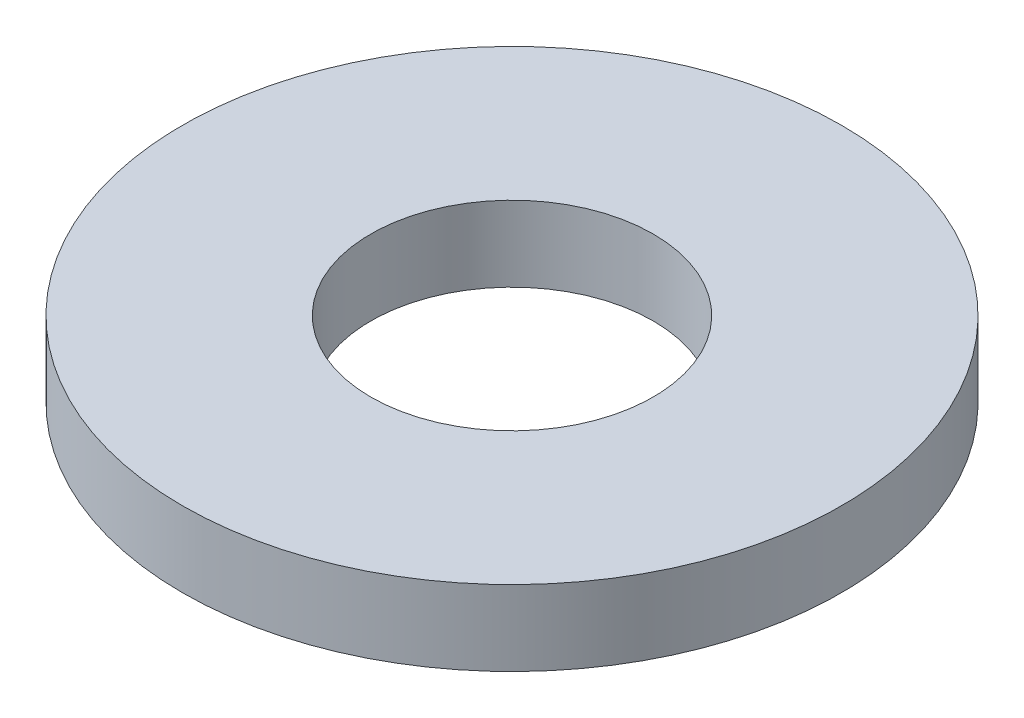
SolidWorks part; units mm, degrees
ref_plane "前视基准面" through (0, 0, 0) normal (0, 0, 1) x (1, 0, 0)
ref_plane "上视基准面" through (0, 0, 0) normal (0, 1, 0) x (1, 0, 0)
ref_plane "右视基准面" through (0, 0, 0) normal (1, 0, 0) x (0, 0, -1)
sketch "草图1" plane through (0, 0, 0) normal (0, 1, 0) x (1, 0, 0)
  circle A0 centre (0, 0) radius 1.5
  circle A1 centre (0, 0) radius 3.5
  dimension "D1" = 3
  dimension "D2" = 7
extrude "凸台-拉伸1" add sketch "草图1" along normal blind 0.8
